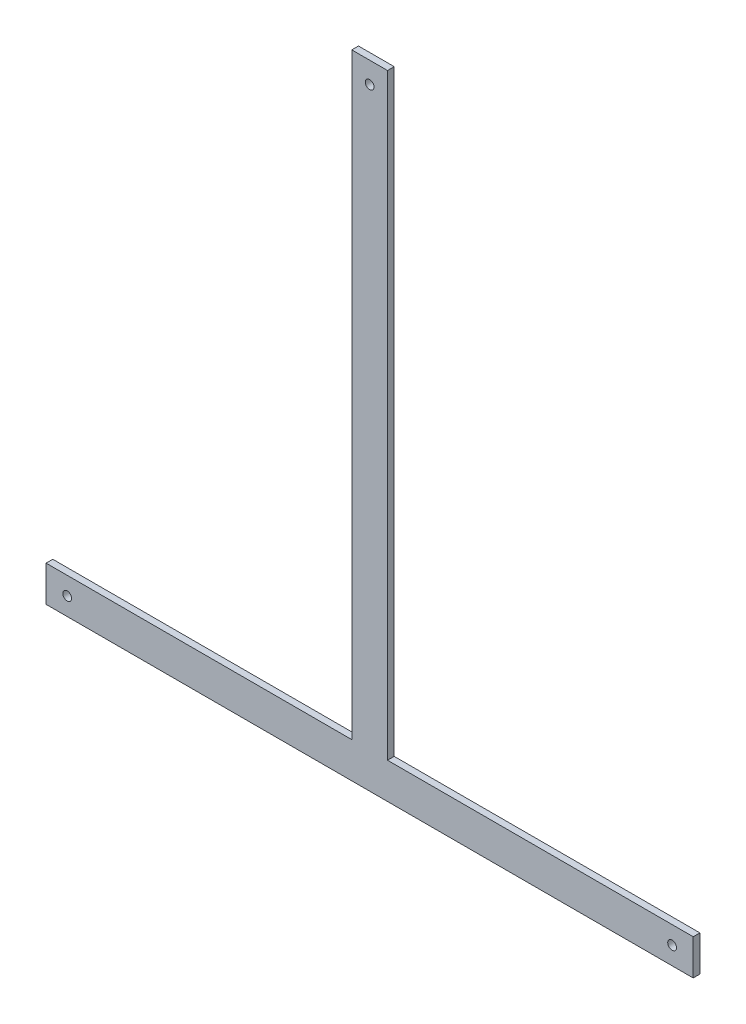
SolidWorks part; units mm, degrees
ref_plane "Front Plane" through (0, 0, 0) normal (0, 0, 1) x (1, 0, 0)
ref_plane "Top Plane" through (0, 0, 0) normal (0, 1, 0) x (1, 0, 0)
ref_plane "Right Plane" through (0, 0, 0) normal (1, 0, 0) x (0, 0, -1)
sketch "Sketch1" plane through (0, 0, 0) normal (0, 0, 1) x (1, 0, 0)
  line L0 (0, 55.6014) -> (0, -59.8118) construction
  line L1 (-230, 0) -> (230, 0)
  line L2 (230, 0) -> (230, 25.4)
  line L3 (230, 25.4) -> (12.7, 25.4)
  line L4 (12.7, 25.4) -> (12.7, 450)
  line L5 (12.7, 450) -> (-12.7, 450)
  line L6 (-12.7, 25.4) -> (-12.7, 450)
  line L7 (-230, 0) -> (-230, 25.4)
  line L8 (-230, 25.4) -> (-12.7, 25.4)
  point P10 (0, 450)
  point P13 (0, 0)
extrude "Extrude1" add sketch "Sketch1" along normal blind 4.7625
sketch "Sketch2" plane through (0, 0, 4.7625) normal (0, 0, 1) x (1, 0, 0)
  line L0 (230, 0) -> (230, 25.4) construction
  line L2 (12.7, 450) -> (-12.7, 450) construction
  circle A0 centre (215, 12.7) radius 3.125
  circle A1 centre (-215, 12.7) radius 3.125
  circle A2 centre (0, 435) radius 3.125
  point P2 (230, 12.7)
  dimension "D3" = 15
  dimension "D4" = 6.25
extrude "Cut-Extrude1" cut sketch "Sketch2" against normal through all
